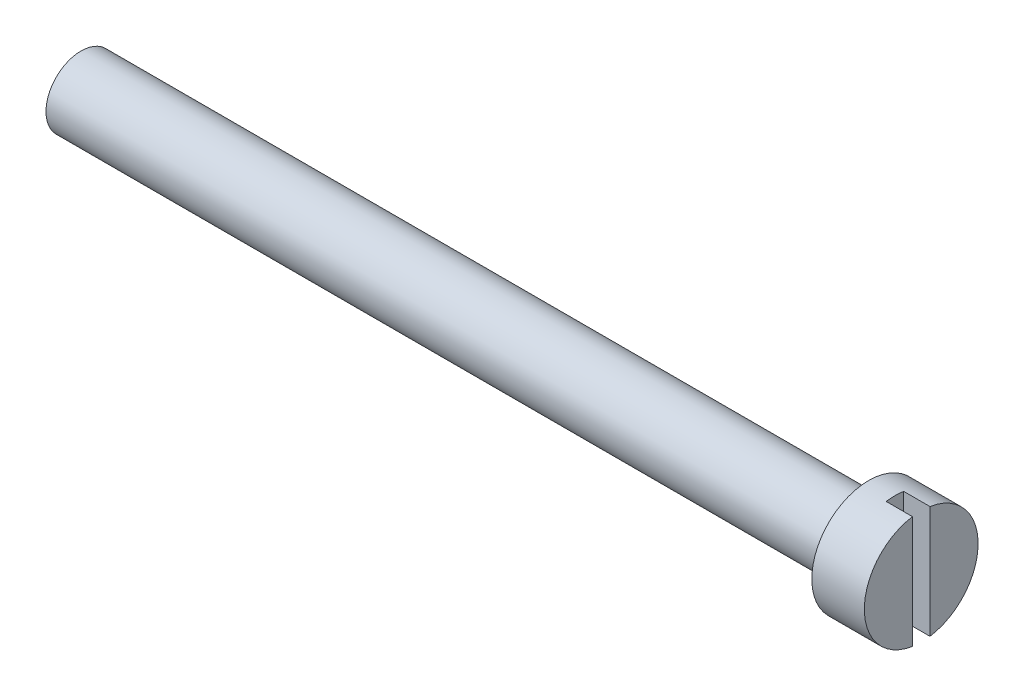
SolidWorks part; units mm, degrees
material "AISI 316 Stainless Steel Sheet (SS)"
ref_plane "Front Plane" through (0, 0, 0) normal (0, 0, 1) x (1, 0, 0)
ref_plane "Top Plane" through (0, 0, 0) normal (0, 1, 0) x (1, 0, 0)
ref_plane "Right Plane" through (0, 0, 0) normal (1, 0, 0) x (0, 0, -1)
sketch "Sketch1" plane through (0, 0, 0) normal (0, 0, 1) x (1, 0, 0)
  line L0 (0, 0) -> (-48, 0)
  line L1 (-48, 0) -> (-48, 2)
  line L2 (-48, 2) -> (-3, 2)
  line L3 (-3, 2) -> (-3, 3.25)
  line L4 (-3, 3.25) -> (0, 3.25)
  line L5 (0, 3.25) -> (0, 0)
  dimension "D1" = 3
  dimension "D2" = 45
  dimension "D3" = 2
  dimension "D4" = 3.25
revolve "Revolve1" add sketch "Sketch1" angle 360 about L0
sketch "Sketch2" plane through (0, 0, 0) normal (1, 0, 0) x (0, 0, -1)
  line L1 (-0.5, -3.25) -> (0.5, -3.25)
  line L2 (-0.5, -3.25) -> (-0.5, 3.25)
  line L3 (-0.5, 3.25) -> (0.5, 3.25)
  line L4 (0.5, -3.25) -> (0.5, 3.25)
  line L5 (-0.5, -3.25) -> (0.5, 3.25) construction
  line L6 (-0.5, 3.25) -> (0.5, -3.25) construction
  circle A0 centre (0, 0) radius 3.25 construction
  point P0 (0, 0)
  dimension "D1" = 1
extrude "Cut-Extrude1" cut sketch "Sketch2" against normal blind 1.5
